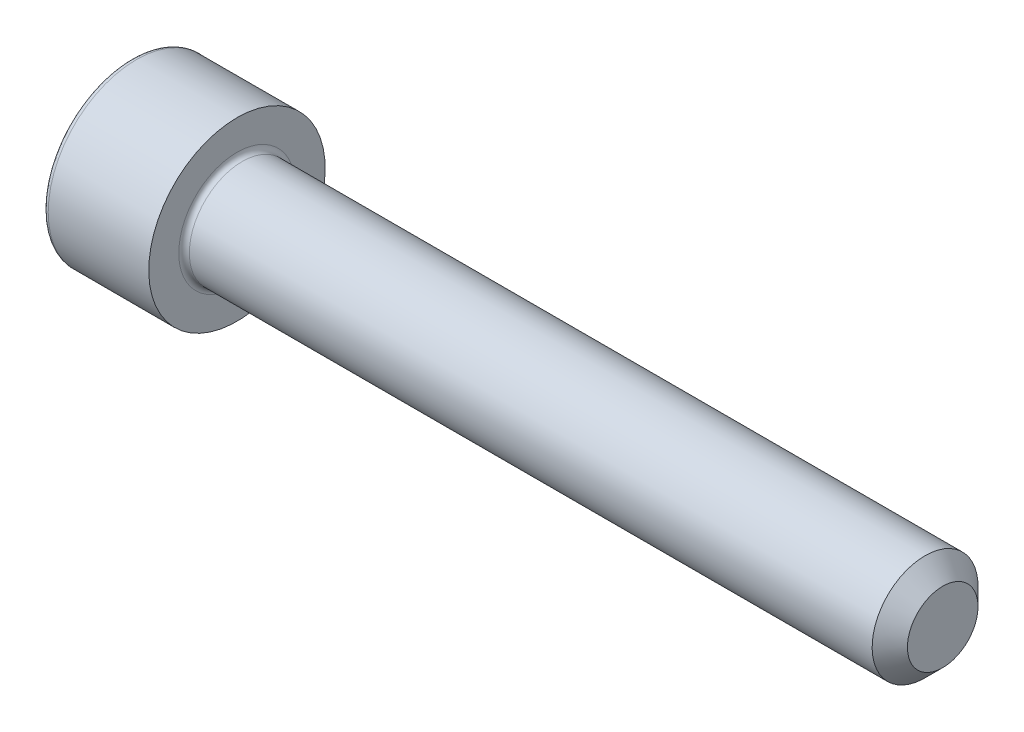
SolidWorks part; units mm, degrees
ref_plane "Спереди" through (0, 0, 0) normal (0, 0, 1) x (1, 0, 0)
ref_plane "Сверху" through (0, 0, 0) normal (0, 1, 0) x (1, 0, 0)
ref_plane "Справа" through (0, 0, 0) normal (1, 0, 0) x (0, 0, -1)
sketch "Эскиз1" plane through (0, 0, 0) normal (0, 0, 1) x (1, 0, 0)
  line L0 (0, 0) -> (0, 5)
  line L1 (0, 5) -> (6, 5)
  line L2 (6, 5) -> (6, 3)
  line L3 (6, 3) -> (46, 3)
  line L4 (46, 3) -> (46, 0)
  line L5 (46, 0) -> (0, 0) construction
  line L6 (0, 0) -> (46, 0)
  dimension "D1" = 10
  dimension "D2" = 6
  dimension "D3" = 6
  dimension "D4" = 40
revolve "Повернуть1" add sketch "Эскиз1" angle 360 about L5
cosmetic thread "Условное изображение резьбы1" parameters "D2"=4.891
sketch "Эскиз2" plane through (0, 0, 0) normal (-1, 0, 0) x (0, 0, 1)
  line L1 (-1.4434, 2.5) -> (-2.8868, 0)
  line L2 (-2.8868, 0) -> (-1.4434, -2.5)
  line L3 (-1.4434, -2.5) -> (1.4434, -2.5)
  line L4 (1.4434, -2.5) -> (2.8868, 0)
  line L5 (2.8868, 0) -> (1.4434, 2.5)
  line L6 (1.4434, 2.5) -> (-1.4434, 2.5)
  circle A0 centre (0, 0) radius 2.5 construction
  dimension "D1" = 5
extrude "Вырез-Вытянуть1" cut sketch "Эскиз2" against normal blind 2.5
fillet "Скругление1" radius 0.3 2 edges at (0, 5, 0) (6, 3, 0)
chamfer "Фаска1" distance 1 angle 45 1 edges at (46, 3, 0)
